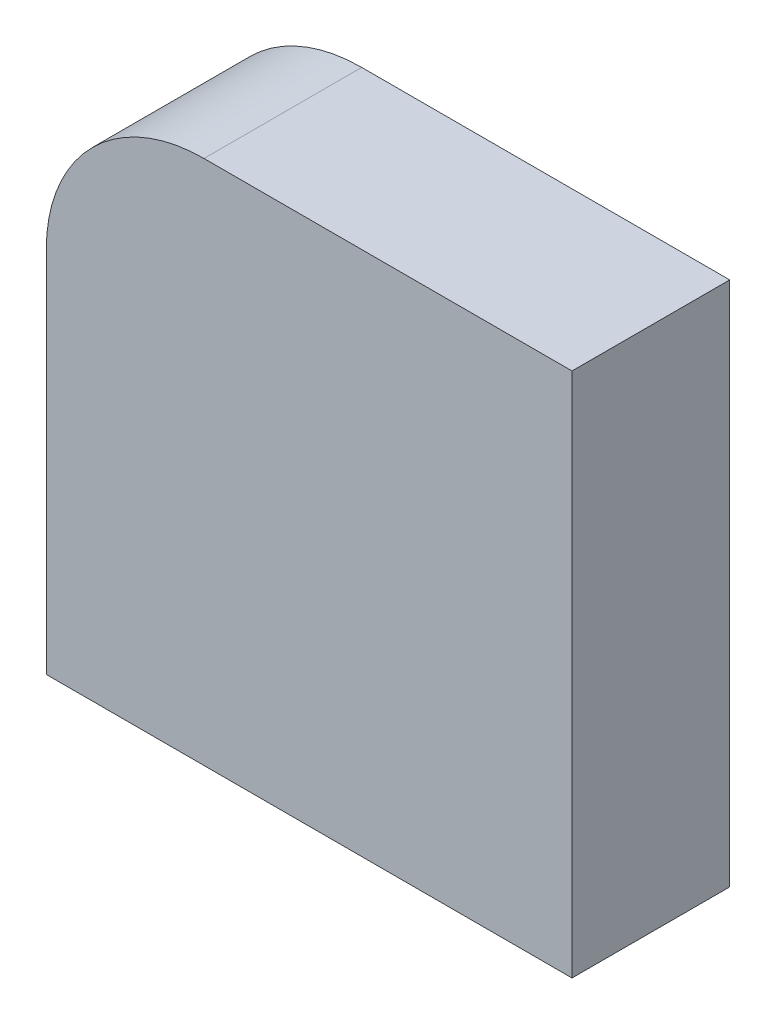
SolidWorks part; units mm, degrees
ref_plane "Front Plane" through (0, 0, 0) normal (0, 0, 1) x (1, 0, 0)
ref_plane "Top Plane" through (0, 0, 0) normal (0, 1, 0) x (1, 0, 0)
ref_plane "Right Plane" through (0, 0, 0) normal (1, 0, 0) x (0, 0, -1)
sketch "Sketch1" plane through (0, 0, 0) normal (0, 0, 1) x (1, 0, 0)
  line L0 (0, 0) -> (0, 254)
  line L1 (0, 254) -> (-177.8, 254)
  line L3 (-254, 177.8) -> (-254, 0)
  line L4 (-254, 0) -> (0, 0)
  arc A0 (-254, 177.8) -> (-177.8, 254) centre (-177.8, 177.8) cw
  dimension "D3" = 76.2
  dimension "D1" = 254
  dimension "D2" = 254
extrude "Boss-Extrude1" add sketch "Sketch1" against normal blind 76.2
